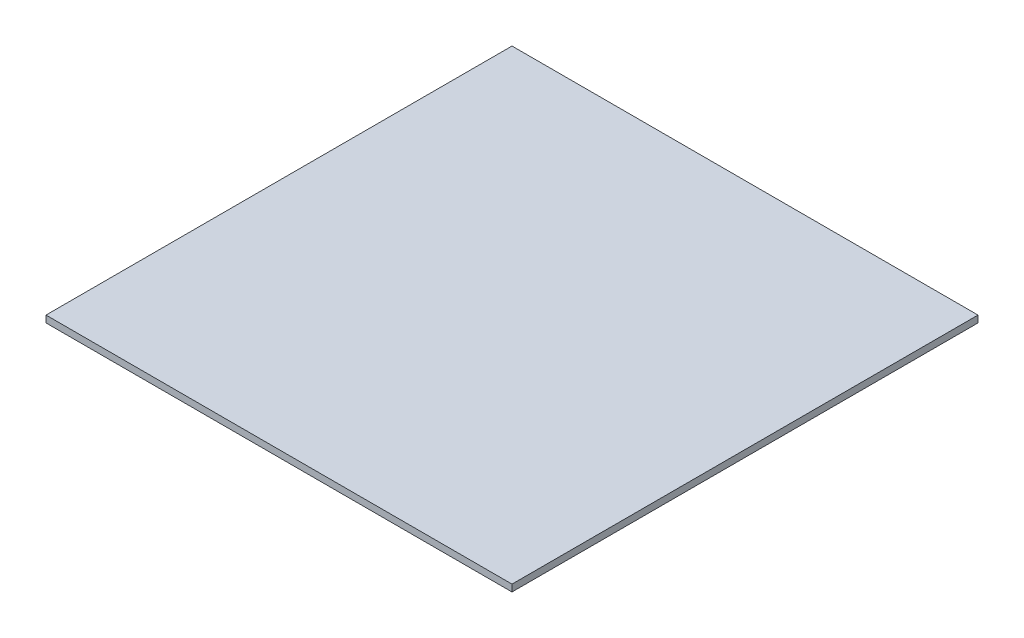
SolidWorks part; units mm, degrees
material "Glass"
ref_plane "Front Plane" through (0, 0, 0) normal (0, 0, 1) x (1, 0, 0)
ref_plane "Top Plane" through (0, 0, 0) normal (0, 1, 0) x (1, 0, 0)
ref_plane "Right Plane" through (0, 0, 0) normal (1, 0, 0) x (0, 0, -1)
sketch "Sketch1" plane through (0, 0, 0) normal (0, 1, 0) x (1, 0, 0)
  line L1 (-37.5, 37.5) -> (37.5, 37.5)
  line L2 (-37.5, 37.5) -> (-37.5, -37.5)
  line L3 (-37.5, -37.5) -> (37.5, -37.5)
  line L4 (37.5, 37.5) -> (37.5, -37.5)
  line L5 (-37.5, 37.5) -> (37.5, -37.5) construction
  line L6 (-37.5, -37.5) -> (37.5, 37.5) construction
  point P0 (0, 0)
  dimension "D1" = 75
extrude "Boss-Extrude1" add sketch "Sketch1" along normal blind 1.1
